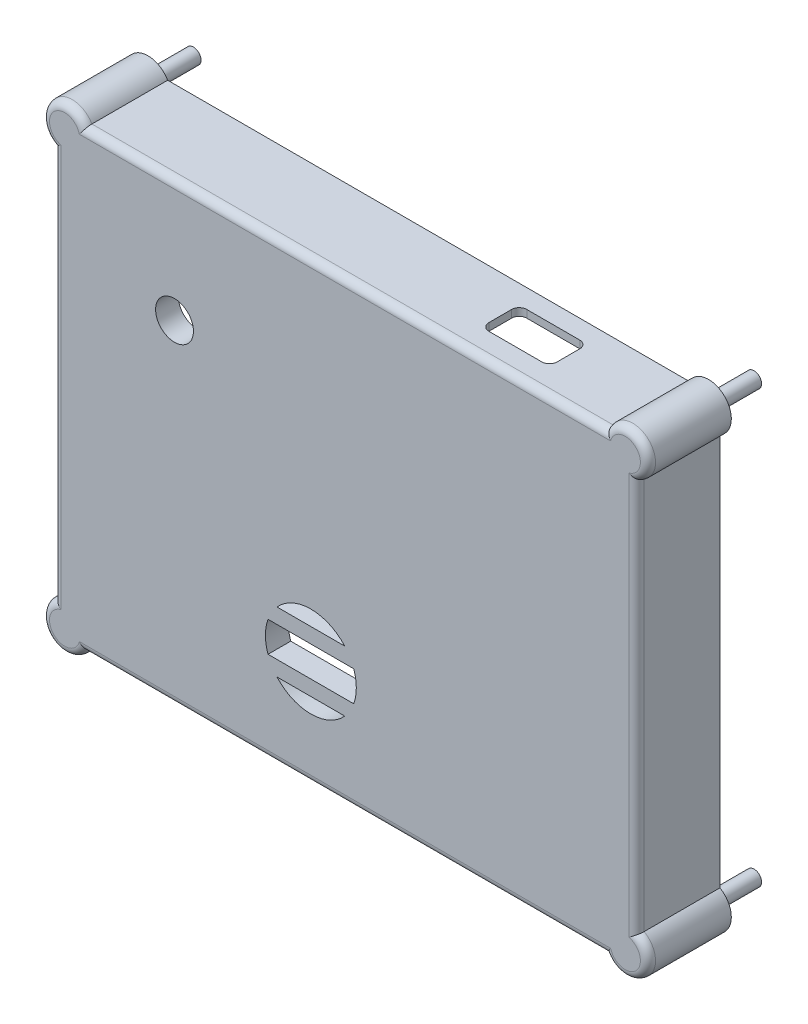
SolidWorks part; units mm, degrees
ref_plane "Front Plane" through (0, 0, 0) normal (0, 0, 1) x (1, 0, 0)
ref_plane "Top Plane" through (0, 0, 0) normal (0, 1, 0) x (1, 0, 0)
ref_plane "Right Plane" through (0, 0, 0) normal (1, 0, 0) x (0, 0, -1)
sketch "Sketch2" plane through (0, 0, 0) normal (0, 0, 1) x (1, 0, 0)
  line L0 (-35.5, -27) -> (35.5, -27) construction
  line L1 (35.5, 27) -> (35.5, -27) construction
  line L2 (-35.5, 27) -> (35.5, 27) construction
  line L3 (-35.5, 27) -> (-35.5, -27) construction
  line L12 (-35.5, -27) -> (-25.5, -27)
  line L13 (35.5, 27) -> (35.5, 17)
  line L14 (-35.5, 27) -> (-25.5, 27)
  line L15 (-35.5, 27) -> (-35.5, 17)
  line L16 (-35.5, -17) -> (-35.5, -27)
  line L17 (25.5, 27) -> (35.5, 27)
  line L18 (35.5, -17) -> (35.5, -27)
  line L19 (25.5, -27) -> (35.5, -27)
  circle A0 centre (33, -23) radius 1.75 construction
  arc A1 (35.5, -17) -> (25.5, -27) centre (35.5, -27) ccw construction
  circle A2 centre (-33, -23) radius 1.75 construction
  arc A3 (-25.5, -27) -> (-35.5, -17) centre (-35.5, -27) ccw construction
  circle A4 centre (33, 21) radius 1.75 construction
  circle A5 centre (-33, 21) radius 1.75 construction
  arc A6 (25.5, 27) -> (35.5, 17) centre (35.5, 27) ccw construction
  arc A7 (-35.5, 17) -> (-25.5, 27) centre (-35.5, 27) ccw construction
  circle A8 centre (33, -23) radius 1.75
  arc A9 (35.5, -17) -> (25.5, -27) centre (35.5, -27) ccw
  circle A10 centre (-33, -23) radius 1.75
  arc A11 (-25.5, -27) -> (-35.5, -17) centre (-35.5, -27) ccw
  circle A12 centre (33, 21) radius 1.75
  circle A13 centre (-33, 21) radius 1.75
  arc A14 (25.5, 27) -> (35.5, 17) centre (35.5, 27) ccw
  arc A15 (-35.5, 17) -> (-25.5, 27) centre (-35.5, 27) ccw
extrude "Boss-Extrude1" add sketch "Sketch2" along normal blind 8 and the other way blind 12
sketch "Sketch3" plane through (0, 0, 0) normal (0, 0, 1) x (1, 0, 0)
  line L0 (-35.5, 27) -> (35.5, 27) construction
  line L1 (35.5, 27) -> (35.5, -27) construction
  line L2 (-35.5, -27) -> (35.5, -27) construction
  line L3 (-35.5, 27) -> (-35.5, -27) construction
  line L4 (38.5, -30) -> (38.5, 30)
  line L5 (38.5, 30) -> (-38.5, 30)
  line L6 (-38.5, 30) -> (-38.5, -30)
  line L7 (-38.5, -30) -> (38.5, -30)
  line L8 (38.5, -30) -> (38.5, 30)
  line L9 (38.5, 30) -> (-38.5, 30)
  line L10 (-38.5, 30) -> (-38.5, -30)
  line L11 (-38.5, -30) -> (38.5, -30)
  line L12 (-35.5, 27) -> (35.5, 27)
  line L13 (35.5, 27) -> (35.5, -27)
  line L14 (-35.5, -27) -> (35.5, -27)
  line L15 (-35.5, 27) -> (-35.5, -27)
  dimension "D1" = 0
extrude "Boss-Extrude2" add sketch "Sketch3" along normal up to surface (8 mm away) up to face at (-31.4763, 22.9763, 8)
sketch "Sketch4" plane through (0, 0, 8) normal (0, 0, 1) x (1, 0, 0)
  line L1 (-38.5, 30) -> (38.5, 30)
  line L2 (-38.5, 30) -> (-38.5, -30)
  line L3 (-38.5, -30) -> (38.5, -30)
  line L4 (38.5, 30) -> (38.5, -30)
extrude "Boss-Extrude3" add sketch "Sketch4" along normal blind 3
sketch "Sketch12" plane through (0, 0, -12) normal (0, 0, -1) x (-1, 0, 0)
  line L0 (-35.5, -27) -> (-25.5, -27) construction
  line L1 (-35.5, -17) -> (-35.5, -27) construction
  line L2 (35.5, -27) -> (35.5, -17) construction
  line L3 (25.5, -27) -> (35.5, -27) construction
  line L4 (35.5, 17) -> (35.5, 27) construction
  line L5 (35.5, 27) -> (25.5, 27) construction
  line L6 (-25.5, 27) -> (-35.5, 27) construction
  line L7 (-35.5, 27) -> (-35.5, 17) construction
  line L8 (-35.5, -27) -> (-25.5, -27)
  line L9 (-35.5, -17) -> (-35.5, -27)
  line L10 (35.5, -27) -> (35.5, -17)
  line L11 (25.5, -27) -> (35.5, -27)
  line L12 (35.5, 17) -> (35.5, 27)
  line L13 (35.5, 27) -> (25.5, 27)
  line L14 (-25.5, 27) -> (-35.5, 27)
  line L15 (-35.5, 27) -> (-35.5, 17)
  arc A0 (-25.5, -27) -> (-35.5, -17) centre (-35.5, -27) ccw construction
  arc A1 (35.5, -17) -> (25.5, -27) centre (35.5, -27) ccw construction
  arc A2 (25.5, 27) -> (35.5, 17) centre (35.5, 27) ccw construction
  arc A3 (-35.5, 17) -> (-25.5, 27) centre (-35.5, 27) ccw construction
  arc A4 (-25.5, -27) -> (-35.5, -17) centre (-35.5, -27) ccw
  arc A5 (35.5, -17) -> (25.5, -27) centre (35.5, -27) ccw
  arc A6 (25.5, 27) -> (35.5, 17) centre (35.5, 27) ccw
  arc A7 (-35.5, 17) -> (-25.5, 27) centre (-35.5, 27) ccw
extrude "Cut-Extrude6" cut sketch "Sketch12" against normal blind 20
sketch "Sketch14" plane through (0, 30, 0) normal (0, 1, 0) x (1, 0, 0)
  line L0 (43.494, -8) -> (-3.6933, -8) construction
  line L1 (35.5, -8) -> (-35.5, -8) construction
  line L2 (35.5, 1.0681) -> (35.5, -19.0592) construction
  line L4 (22.5, -7.5) -> (15.5, -7.5)
  line L5 (23.5, -6.5) -> (23.5, -3.5)
  line L6 (22.5, -2.5) -> (15.5, -2.5)
  line L7 (14.5, -6.5) -> (14.5, -3.5)
  arc A0 (22.5, -7.5) -> (23.5, -6.5) centre (22.5, -6.5) ccw
  arc A1 (15.5, -7.5) -> (14.5, -6.5) centre (15.5, -6.5) cw
  arc A2 (23.5, -3.5) -> (22.5, -2.5) centre (22.5, -3.5) ccw
  arc A3 (14.5, -3.5) -> (15.5, -2.5) centre (15.5, -3.5) cw
  point P14 (14.5, -7.5)
  point P17 (23.5, -2.5)
  point P20 (14.5, -2.5)
  dimension "D5" = 1
  dimension "D1" = 9
  dimension "D2" = 5
  dimension "D3" = 12
  dimension "D4" = 0.5
extrude "Cut-Extrude8" cut sketch "Sketch14" against normal blind 13
sketch "Sketch15" plane through (0, 0, 11) normal (0, 0, 1) x (1, 0, 0)
  line L0 (-35.5, -27) -> (5.9753, -27) construction
  line L1 (-35.5, -27) -> (35.5, -27) construction
  line L2 (-35.5, -27) -> (-35.5, 0) construction
  line L3 (-10.5, -16) -> (1.5, -16) construction
  line L4 (-8.9721, -12) -> (-0.0279, -12)
  line L5 (-10.1569, -14) -> (1.1569, -14)
  line L6 (-0.0279, -20) -> (-8.9721, -20)
  line L7 (1.1569, -18) -> (-10.1569, -18)
  circle A0 centre (-4.5, -16) radius 6
  dimension "D3" = 12
  dimension "D1" = 11
  dimension "D2" = 31
  dimension "D4" = 4
  dimension "D5" = 2
  dimension "D6" = 2
  dimension "D7" = 4
extrude "Cut-Extrude9" cut sketch "Sketch15" against normal blind 10 contours L4 A0 | L5 A0 L7 | L6 A0
sketch "Sketch17" plane through (0, 0, 0) normal (0, 0, -1) x (-1, 0, 0)
  line L0 (38.5, -30) -> (-38.5, -30) construction
  line L1 (-38.5, 30) -> (38.5, 30) construction
  line L2 (-38.5, -30) -> (-38.5, 30) construction
  line L3 (38.5, 30) -> (38.5, -30) construction
  circle A0 centre (-37, 28.5) radius 1
  circle A1 centre (37, 28.5) radius 1
  circle A2 centre (37, -28.5) radius 1
  circle A3 centre (-37, -28.4728) radius 1
  dimension "D1" = 2
  dimension "D2" = 1.5
  dimension "D3" = 1.5
  dimension "D4" = 1.5
  dimension "D5" = 1.5
  dimension "D6" = 1.5
extrude "Boss-Extrude5" add sketch "Sketch17" along normal blind 6 and the other way blind 7
fillet "Fillet1" radius 1 4 edges at (38.5, -30, 5.5) (-38.5, -30, 5.5) (-38.5, 30, 5.5) (38.5, 30, 5.5)
sketch "Sketch19" plane through (0, 0, 0) normal (0, 0, -1) x (-1, 0, 0)
  line L0 (38.5, 29) -> (38.5, -29) construction
  line L1 (37.5, -30) -> (-37.5, -30) construction
  line L2 (-38.5, -29) -> (-38.5, 29) construction
  line L3 (-37.5, 30) -> (37.5, 30) construction
  line L4 (38.5, 29) -> (38.5, 25.9019)
  line L5 (37.5, -30) -> (34.4019, -30)
  line L6 (-38.5, -29) -> (-38.5, -25.8747)
  line L7 (-37.5, 30) -> (-34.4019, 30)
  line L8 (34.4019, 30) -> (37.5, 30)
  line L9 (-38.5, 25.9019) -> (-38.5, 29)
  line L10 (-34.4178, -30) -> (-37.5, -30)
  line L11 (38.5, -25.9019) -> (38.5, -29)
  arc A0 (38.5, 29) -> (37.5, 30) centre (37.5, 29) ccw construction
  arc A1 (37.5, -30) -> (38.5, -29) centre (37.5, -29) ccw construction
  arc A2 (-38.5, -29) -> (-37.5, -30) centre (-37.5, -29) ccw construction
  arc A3 (-37.5, 30) -> (-38.5, 29) centre (-37.5, 29) ccw construction
  arc A4 (38.5, 29) -> (37.5, 30) centre (37.5, 29) ccw
  arc A5 (37.5, -30) -> (38.5, -29) centre (37.5, -29) ccw
  arc A6 (-38.5, -29) -> (-37.5, -30) centre (-37.5, -29) ccw
  arc A7 (-37.5, 30) -> (-38.5, 29) centre (-37.5, 29) ccw
  arc A8 (-34.4019, 30) -> (-38.5, 25.9019) centre (-37, 28.5) ccw
  arc A9 (38.5, 25.9019) -> (34.4019, 30) centre (37, 28.5) ccw
  arc A10 (34.4019, -30) -> (38.5, -25.9019) centre (37, -28.5) ccw
  arc A11 (-38.5, -25.8747) -> (-34.4178, -30) centre (-37, -28.4728) ccw
  dimension "D1" = 6
extrude "Boss-Extrude6" add sketch "Sketch19" against normal up to surface (11 mm away) up to face at (-4.5, -11, 11)
fillet "Fillet3" radius 1 8 edges at (39.1324, -30.5829, 11) (38.5, 0.0136, 11) (39.1213, 30.6213, 11) (0.008, -30, 11) (-39.1213, -30.6213, 11) (-38.5, 0, 11) (-39.1213, 30.6213, 11) (0, 30, 11)
sketch "Sketch20" plane through (0, 0, 11) normal (0, 0, 1) x (1, 0, 0)
  line L0 (-37.5, 26.5635) -> (-37.5, -26.5635) construction
  line L1 (35.0635, 29) -> (-35.0635, 29) construction
  circle A0 centre (-22.5, 14) radius 2.5
  dimension "D1" = 5
  dimension "D2" = 15
  dimension "D3" = 15
extrude "Cut-Extrude10" cut sketch "Sketch20" against normal blind 10
sketch "Sketch22" plane through (0, 0, 0) normal (0, 0, -1) x (-1, 0, 0)
  line L0 (-35.5, 27) -> (35.5, 27) construction
  line L1 (-34.4019, 27) -> (0, 27)
  line L2 (-34.4019, 27) -> (-34.4019, 29)
  line L3 (-34.4019, 29) -> (0, 29)
  line L4 (0, 27) -> (0, 29)
  dimension "D1" = 2
extrude "Cut-Extrude11" cut sketch "Sketch22" against normal blind 8
